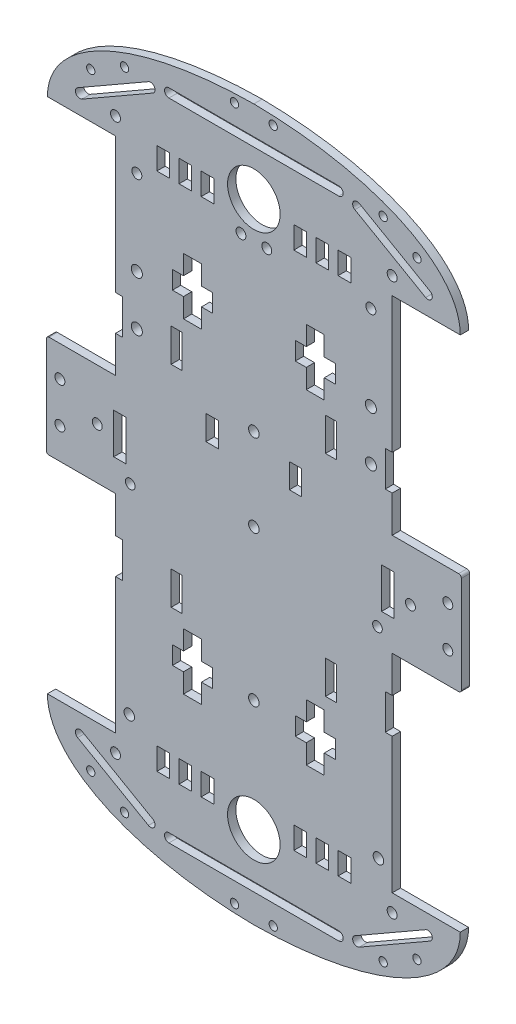
SolidWorks part; units mm, degrees
ref_plane "Front Plane" through (0, 0, 0) normal (0, 0, 1) x (1, 0, 0)
ref_plane "Top Plane" through (0, 0, 0) normal (0, 1, 0) x (1, 0, 0)
ref_plane "Right Plane" through (0, 0, 0) normal (1, 0, 0) x (0, 0, -1)
ref_plane "Plane1" through (0, 0, 3) normal (0, 0, 1) x (1, 0, 0)
sketch "Sketch1" plane through (0, 0, 3) normal (0, 0, 1) x (1, 0, 0)
  line L0 (-206.205, 97.9605) -> (-201.605, 97.9605)
  line L1 (-201.605, 97.9605) -> (-201.605, 89.9605)
  line L2 (-201.605, 89.9605) -> (-206.205, 89.9605)
  line L3 (-206.205, 89.9605) -> (-206.205, 97.9605)
  line L4 (-214.205, 97.9605) -> (-209.605, 97.9605)
  line L5 (-209.605, 97.9605) -> (-209.605, 89.9605)
  line L6 (-209.605, 89.9605) -> (-214.205, 89.9605)
  line L7 (-214.205, 89.9605) -> (-214.205, 97.9605)
  line L8 (-217.605, 89.9605) -> (-222.205, 89.9605)
  line L9 (-222.205, 89.9605) -> (-222.205, 97.9605)
  line L10 (-222.205, 97.9605) -> (-217.605, 97.9605)
  line L11 (-217.605, 97.9605) -> (-217.605, 89.9605)
  line L12 (-212.5961, 55.4834) -> (-216.5834, 55.4834)
  line L13 (-216.5834, 55.4834) -> (-216.5834, 61.9834)
  line L14 (-216.5834, 61.9834) -> (-212.5961, 61.9834)
  line L15 (-212.5961, 61.9834) -> (-212.5961, 68.9834)
  line L16 (-212.5961, 68.9834) -> (-206.0961, 68.9834)
  line L17 (-206.0961, 68.9834) -> (-206.0961, 61.9834)
  line L18 (-206.0961, 61.9834) -> (-202.1292, 61.9834)
  line L19 (-202.1292, 61.9834) -> (-202.1292, 55.4834)
  line L20 (-202.1292, 55.4834) -> (-206.0961, 55.4834)
  line L21 (-206.0961, 55.4834) -> (-206.0961, 48.4834)
  line L22 (-206.0961, 48.4834) -> (-212.5961, 48.4834)
  line L23 (-212.5961, 48.4834) -> (-212.5961, 55.4834)
  line L24 (-199.9648, 14.1027) -> (-204.4648, 14.1027)
  line L25 (-204.4648, 14.1027) -> (-204.4648, 22.9668)
  line L26 (-204.4648, 22.9668) -> (-199.9648, 22.9668)
  line L27 (-199.9648, 22.9668) -> (-199.9648, 14.1027)
  line L28 (-213.0509, 32.0251) -> (-217.0509, 32.0251)
  line L29 (-217.0509, 32.0251) -> (-217.0509, 44.0251)
  line L30 (-217.0509, 44.0251) -> (-213.0509, 44.0251)
  line L31 (-213.0509, 44.0251) -> (-213.0509, 32.0251)
  line L32 (-250.8438, 101.7215) -> (-225.2572, 116.4076)
  line L33 (-223.6642, 113.6322) -> (-249.2509, 98.9462)
  line L34 (-125.058, 98.9462) -> (-150.6447, 113.6322)
  line L35 (-149.0517, 116.4076) -> (-123.4651, 101.7215)
  line L36 (-157.2579, 32.0251) -> (-161.2579, 32.0251)
  line L37 (-161.2579, 32.0251) -> (-161.2579, 44.0251)
  line L38 (-161.2579, 44.0251) -> (-157.2579, 44.0251)
  line L39 (-157.2579, 44.0251) -> (-157.2579, 32.0251)
  line L40 (-169.844, 14.1027) -> (-174.344, 14.1027)
  line L41 (-174.344, 14.1027) -> (-174.344, 22.9668)
  line L42 (-174.344, 22.9668) -> (-169.844, 22.9668)
  line L43 (-169.844, 22.9668) -> (-169.844, 14.1027)
  line L44 (-157.7255, 55.4834) -> (-161.7128, 55.4834)
  line L45 (-161.7128, 55.4834) -> (-161.7128, 48.4834)
  line L46 (-161.7128, 48.4834) -> (-168.2128, 48.4834)
  line L47 (-168.2128, 48.4834) -> (-168.2128, 55.4834)
  line L48 (-168.2128, 55.4834) -> (-172.1797, 55.4834)
  line L49 (-172.1797, 55.4834) -> (-172.1797, 61.9834)
  line L50 (-172.1797, 61.9834) -> (-168.2128, 61.9834)
  line L51 (-168.2128, 61.9834) -> (-168.2128, 68.9834)
  line L52 (-168.2128, 68.9834) -> (-161.7128, 68.9834)
  line L53 (-161.7128, 68.9834) -> (-161.7128, 61.9834)
  line L54 (-161.7128, 61.9834) -> (-157.7255, 61.9834)
  line L55 (-157.7255, 61.9834) -> (-157.7255, 55.4834)
  line L56 (-152.1039, 89.9605) -> (-156.7039, 89.9605)
  line L57 (-156.7039, 89.9605) -> (-156.7039, 97.9605)
  line L58 (-156.7039, 97.9605) -> (-152.1039, 97.9605)
  line L59 (-152.1039, 97.9605) -> (-152.1039, 89.9605)
  line L60 (-164.7039, 97.9605) -> (-160.1039, 97.9605)
  line L61 (-160.1039, 97.9605) -> (-160.1039, 89.9605)
  line L62 (-160.1039, 89.9605) -> (-164.7039, 89.9605)
  line L63 (-164.7039, 89.9605) -> (-164.7039, 97.9605)
  line L64 (-172.7039, 97.9605) -> (-168.1039, 97.9605)
  line L65 (-168.1039, 97.9605) -> (-168.1039, 89.9605)
  line L66 (-168.1039, 89.9605) -> (-172.7039, 89.9605)
  line L67 (-172.7039, 89.9605) -> (-172.7039, 97.9605)
  line L68 (-217.8534, 118.1902) -> (-156.4555, 118.1902)
  line L69 (-156.4555, 114.9902) -> (-217.8534, 114.9902)
  line L70 (-249.2509, -98.9462) -> (-223.6642, -113.6322)
  line L71 (-225.2572, -116.4076) -> (-250.8438, -101.7215)
  line L72 (-217.0509, -32.0251) -> (-213.0509, -32.0251)
  line L73 (-213.0509, -32.0251) -> (-213.0509, -44.0251)
  line L74 (-213.0509, -44.0251) -> (-217.0509, -44.0251)
  line L75 (-217.0509, -44.0251) -> (-217.0509, -32.0251)
  line L76 (-216.5834, -55.4834) -> (-212.5961, -55.4834)
  line L77 (-212.5961, -55.4834) -> (-212.5961, -48.4834)
  line L78 (-212.5961, -48.4834) -> (-206.0961, -48.4834)
  line L79 (-206.0961, -48.4834) -> (-206.0961, -55.4834)
  line L80 (-206.0961, -55.4834) -> (-202.1292, -55.4834)
  line L81 (-202.1292, -55.4834) -> (-202.1292, -61.9834)
  line L82 (-202.1292, -61.9834) -> (-206.0961, -61.9834)
  line L83 (-206.0961, -61.9834) -> (-206.0961, -68.9834)
  line L84 (-206.0961, -68.9834) -> (-212.5961, -68.9834)
  line L85 (-212.5961, -68.9834) -> (-212.5961, -61.9834)
  line L86 (-212.5961, -61.9834) -> (-216.5834, -61.9834)
  line L87 (-216.5834, -61.9834) -> (-216.5834, -55.4834)
  line L88 (-222.205, -89.9605) -> (-217.605, -89.9605)
  line L89 (-217.605, -89.9605) -> (-217.605, -97.9605)
  line L90 (-217.605, -97.9605) -> (-222.205, -97.9605)
  line L91 (-222.205, -97.9605) -> (-222.205, -89.9605)
  line L92 (-209.605, -97.9605) -> (-214.205, -97.9605)
  line L93 (-214.205, -97.9605) -> (-214.205, -89.9605)
  line L94 (-214.205, -89.9605) -> (-209.605, -89.9605)
  line L95 (-209.605, -89.9605) -> (-209.605, -97.9605)
  line L96 (-201.605, -97.9605) -> (-206.205, -97.9605)
  line L97 (-206.205, -97.9605) -> (-206.205, -89.9605)
  line L98 (-206.205, -89.9605) -> (-201.605, -89.9605)
  line L99 (-201.605, -89.9605) -> (-201.605, -97.9605)
  line L100 (-233.296, 7.3) -> (-233.296, -7.3)
  line L101 (-233.296, -7.3) -> (-237.796, -7.3)
  line L102 (-237.796, -7.3) -> (-237.796, 7.3)
  line L103 (-237.796, 7.3) -> (-233.296, 7.3)
  line L104 (-136.5129, 7.3) -> (-136.5129, -7.3)
  line L105 (-136.5129, -7.3) -> (-141.0129, -7.3)
  line L106 (-141.0129, -7.3) -> (-141.0129, 7.3)
  line L107 (-141.0129, 7.3) -> (-136.5129, 7.3)
  line L108 (-123.4651, -101.7215) -> (-149.0517, -116.4076)
  line L109 (-150.6447, -113.6322) -> (-125.058, -98.9462)
  line L110 (-161.2579, -32.0251) -> (-157.2579, -32.0251)
  line L111 (-157.2579, -32.0251) -> (-157.2579, -44.0251)
  line L112 (-157.2579, -44.0251) -> (-161.2579, -44.0251)
  line L113 (-161.2579, -44.0251) -> (-161.2579, -32.0251)
  line L114 (-161.7128, -55.4834) -> (-157.7255, -55.4834)
  line L115 (-157.7255, -55.4834) -> (-157.7255, -61.9834)
  line L116 (-157.7255, -61.9834) -> (-161.7128, -61.9834)
  line L117 (-161.7128, -61.9834) -> (-161.7128, -68.9834)
  line L118 (-161.7128, -68.9834) -> (-168.2128, -68.9834)
  line L119 (-168.2128, -68.9834) -> (-168.2128, -61.9834)
  line L120 (-168.2128, -61.9834) -> (-172.1797, -61.9834)
  line L121 (-172.1797, -61.9834) -> (-172.1797, -55.4834)
  line L122 (-172.1797, -55.4834) -> (-168.2128, -55.4834)
  line L123 (-168.2128, -55.4834) -> (-168.2128, -48.4834)
  line L124 (-168.2128, -48.4834) -> (-161.7128, -48.4834)
  line L125 (-161.7128, -48.4834) -> (-161.7128, -55.4834)
  line L126 (-156.7039, -89.9605) -> (-152.1039, -89.9605)
  line L127 (-152.1039, -89.9605) -> (-152.1039, -97.9605)
  line L128 (-152.1039, -97.9605) -> (-156.7039, -97.9605)
  line L129 (-156.7039, -97.9605) -> (-156.7039, -89.9605)
  line L130 (-160.1039, -97.9605) -> (-164.7039, -97.9605)
  line L131 (-164.7039, -97.9605) -> (-164.7039, -89.9605)
  line L132 (-164.7039, -89.9605) -> (-160.1039, -89.9605)
  line L133 (-160.1039, -89.9605) -> (-160.1039, -97.9605)
  line L134 (-168.1039, -97.9605) -> (-172.7039, -97.9605)
  line L135 (-172.7039, -97.9605) -> (-172.7039, -89.9605)
  line L136 (-172.7039, -89.9605) -> (-168.1039, -89.9605)
  line L137 (-168.1039, -89.9605) -> (-168.1039, -97.9605)
  line L138 (-156.4555, -118.1902) -> (-217.8534, -118.1902)
  line L139 (-217.8534, -114.9902) -> (-156.4555, -114.9902)
  line L140 (-139.6544, 44.4469) -> (-137.1544, 44.4469)
  line L141 (-137.1544, 44.4469) -> (-137.1544, 93.463)
  line L142 (-137.1544, 93.463) -> (-112.5426, 93.463)
  line L143 (-261.7663, 93.463) -> (-237.1544, 93.463)
  line L144 (-237.1544, 93.463) -> (-237.1544, 44.4469)
  line L145 (-237.1544, 44.4469) -> (-234.6544, 44.4469)
  line L146 (-234.6544, 44.4469) -> (-234.6544, 31.679)
  line L147 (-234.6544, 31.679) -> (-237.1544, 31.679)
  line L148 (-237.1544, 31.679) -> (-237.1544, 18.463)
  line L149 (-237.1544, 18.463) -> (-261.1544, 18.463)
  line L150 (-262.1544, 17.463) -> (-262.1544, -17.463)
  line L151 (-261.1544, -18.463) -> (-237.1544, -18.463)
  line L152 (-237.1544, -18.463) -> (-237.1544, -31.679)
  line L153 (-237.1544, -31.679) -> (-234.6544, -31.679)
  line L154 (-234.6544, -31.679) -> (-234.6544, -44.4469)
  line L155 (-234.6544, -44.4469) -> (-237.1544, -44.4469)
  line L156 (-237.1544, -44.4469) -> (-237.1544, -93.463)
  line L157 (-237.1544, -93.463) -> (-261.7663, -93.463)
  line L158 (-112.5426, -93.463) -> (-137.1544, -93.463)
  line L159 (-137.1544, -93.463) -> (-137.1544, -44.4469)
  line L160 (-137.1544, -44.4469) -> (-139.6544, -44.4469)
  line L161 (-139.6544, -44.4469) -> (-139.6544, -31.679)
  line L162 (-139.6544, -31.679) -> (-137.1544, -31.679)
  line L163 (-137.1544, -31.679) -> (-137.1544, -18.463)
  line L164 (-137.1544, -18.463) -> (-113.1544, -18.463)
  line L165 (-112.1544, -17.463) -> (-112.1544, 17.463)
  line L166 (-113.1544, 18.463) -> (-137.1544, 18.463)
  line L167 (-137.1544, 18.463) -> (-137.1544, 31.679)
  line L168 (-137.1544, 31.679) -> (-139.6544, 31.679)
  line L169 (-139.6544, 31.679) -> (-139.6544, 44.4469)
  circle A0 centre (-187.1544, 98.6872) radius 9.5
  circle A1 centre (-229.4513, 36.918) radius 2
  circle A2 centre (-229.4494, 54.918) radius 2
  circle A3 centre (-257.2611, 7.3) radius 1.8
  circle A4 centre (-194.1544, 125.3171) radius 1.5
  circle A5 centre (-233.8982, 116.6652) radius 1.5
  circle A6 centre (-246.1106, 109.82) radius 1.5
  arc A7 (-249.2509, 98.9462) -> (-250.8438, 101.7215) centre (-250.0473, 100.3339) cw
  arc A8 (-225.2572, 116.4076) -> (-223.6642, 113.6322) centre (-224.4607, 115.0199) cw
  circle A9 centre (-237.1488, 99.7255) radius 1.8
  circle A10 centre (-229.446, 85.6107) radius 1.8
  circle A11 centre (-191.8205, 85.6065) radius 1.8
  circle A12 centre (-182.4884, 85.6065) radius 1.8
  circle A13 centre (-144.8629, 85.6107) radius 1.8
  circle A14 centre (-137.1601, 99.7255) radius 1.8
  arc A15 (-123.4651, 101.7215) -> (-125.058, 98.9462) centre (-124.2615, 100.3339) cw
  arc A16 (-150.6447, 113.6322) -> (-149.0517, 116.4076) centre (-149.8482, 115.0199) cw
  circle A17 centre (-128.1982, 109.82) radius 1.5
  circle A18 centre (-140.4106, 116.6652) radius 1.5
  circle A19 centre (-180.1544, 125.3171) radius 1.5
  circle A20 centre (-117.0478, 7.3) radius 1.8
  circle A21 centre (-144.8595, 54.918) radius 2
  circle A22 centre (-144.8575, 36.918) radius 2
  arc A23 (-156.4555, 118.1902) -> (-156.4555, 114.9902) centre (-156.4555, 116.5902) cw
  arc A24 (-217.8534, 114.9902) -> (-217.8534, 118.1902) centre (-217.8534, 116.5902) cw
  circle A25 centre (-243.7479, 0) radius 1.8
  circle A26 centre (-237.1488, -99.7255) radius 1.8
  arc A27 (-250.8438, -101.7215) -> (-249.2509, -98.9462) centre (-250.0473, -100.3339) cw
  arc A28 (-223.6642, -113.6322) -> (-225.2572, -116.4076) centre (-224.4607, -115.0199) cw
  circle A29 centre (-246.1106, -109.82) radius 1.5
  circle A30 centre (-233.8982, -116.6652) radius 1.5
  circle A31 centre (-194.1544, -125.3171) radius 1.5
  circle A32 centre (-257.2611, -7.3) radius 1.8
  circle A33 centre (-137.1601, -99.7255) radius 1.8
  arc A34 (-125.058, -98.9462) -> (-123.4651, -101.7215) centre (-124.2615, -100.3339) cw
  arc A35 (-149.0517, -116.4076) -> (-150.6447, -113.6322) centre (-149.8482, -115.0199) cw
  circle A36 centre (-128.1982, -109.82) radius 1.5
  circle A37 centre (-140.4106, -116.6652) radius 1.5
  circle A38 centre (-180.1544, -125.3171) radius 1.5
  circle A39 centre (-117.0478, -7.3) radius 1.8
  circle A40 centre (-187.1544, -98.6872) radius 9.5
  arc A41 (-217.8534, -118.1902) -> (-217.8534, -114.9902) centre (-217.8534, -116.5902) cw
  arc A42 (-156.4555, -114.9902) -> (-156.4555, -118.1902) centre (-156.4555, -116.5902) cw
  circle A43 centre (-130.561, 0) radius 1.8
  circle A44 centre (-232.1814, -85.1446) radius 1.9
  circle A45 centre (-142.4742, -12.7883) radius 1.75
  circle A46 centre (-187.1544, -3.8693) radius 1.9
  circle A47 centre (-142.1275, -85.1446) radius 1.9
  circle A48 centre (-231.8346, -12.7883) radius 1.75
  circle A49 centre (-187.1544, 25.9492) radius 1.9
  circle A50 centre (-187.1544, -58.1845) radius 1.9
  arc A51 (-261.1544, 18.463) -> (-262.1544, 17.463) centre (-261.1544, 17.463) ccw
  arc A52 (-262.1544, -17.463) -> (-261.1544, -18.463) centre (-261.1544, -17.463) ccw
  arc A53 (-113.1544, -18.463) -> (-112.1544, -17.463) centre (-113.1544, -17.463) ccw
  arc A54 (-112.1544, 17.463) -> (-113.1544, 18.463) centre (-113.1544, 17.463) ccw
  ellipse E0 centre (-207.0703, 85.3503) end of major axis (-301.4914, 75.2537) minor radius 42.2034 (-112.5426, 93.463) -> (-187.1544, 128.5) ccw
  ellipse E1 centre (-167.2386, 85.3503) end of major axis (-261.6597, 95.447) minor radius 42.2034 (-187.1544, 128.5) -> (-261.7663, 93.463) ccw
  ellipse E2 centre (-167.2386, -85.3503) end of major axis (-261.6597, -95.447) minor radius 42.2034 (-261.7663, -93.463) -> (-187.1544, -128.5) ccw
  ellipse E3 centre (-207.0703, -85.3503) end of major axis (-112.6492, -95.447) minor radius 42.2034 (-187.1544, -128.5) -> (-112.5426, -93.463) ccw
  point P246 (-207.0703, 85.3503)
  point P247 (-112.6492, 95.447)
  point P248 (-211.5576, 127.3145)
  point P249 (-112.5426, 93.463)
  point P250 (-187.1544, 128.5)
  point P251 (-138.4649, 120.3833)
  point P252 (-275.6757, 50.3174)
  point P259 (-167.2386, 85.3503)
  point P260 (-72.8174, 75.2537)
  point P261 (-171.7259, 43.3862)
  point P262 (-187.1544, 128.5)
  point P263 (-261.7663, 93.463)
  point P264 (-235.844, 120.3833)
  point P265 (-98.6331, 50.3174)
  point P291 (-167.2386, -85.3503)
  point P292 (-72.8174, -75.2537)
  point P293 (-171.7259, -43.3862)
  point P294 (-261.7663, -93.463)
  point P295 (-187.1544, -128.5)
  point P296 (-235.844, -120.3833)
  point P297 (-98.6331, -50.3174)
  point P304 (-207.0703, -85.3503)
  point P305 (-112.6492, -95.447)
  point P306 (-211.5576, -127.3145)
  point P307 (-187.1544, -128.5)
  point P308 (-112.5426, -93.463)
  point P309 (-138.4649, -120.3833)
  point P310 (-275.6757, -50.3174)
extrude "Boss-Extrude1" add sketch "Sketch1" against normal blind 3
